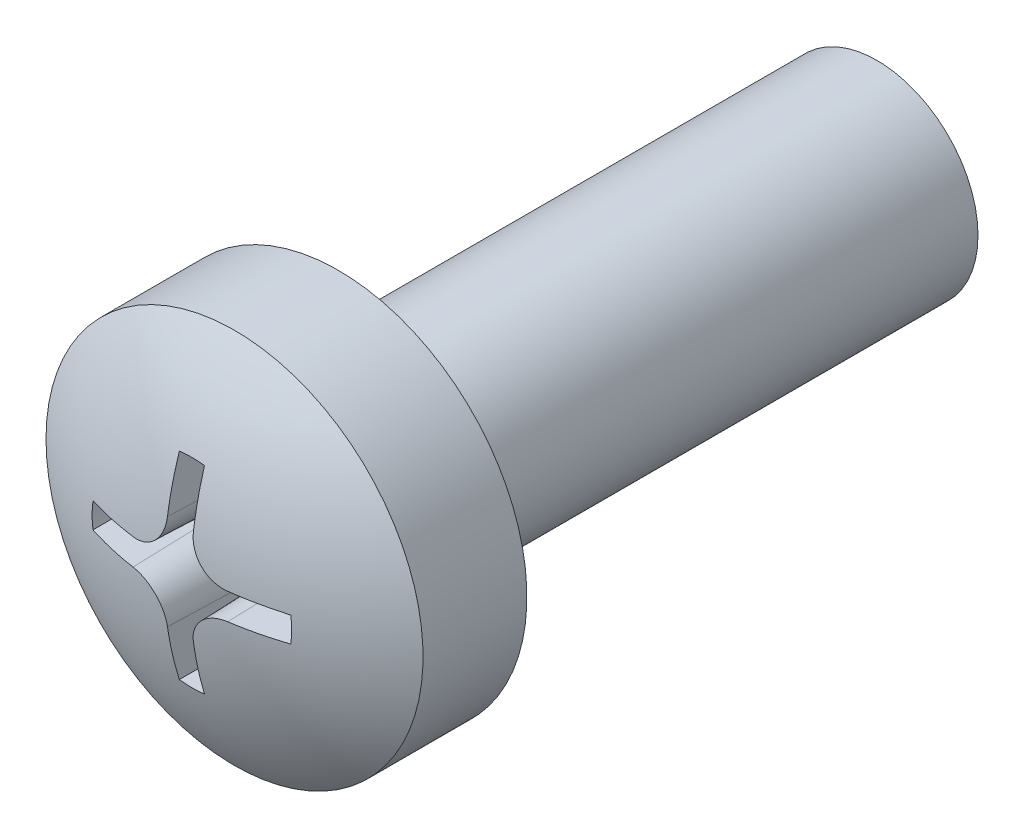
SolidWorks part; units mm, degrees
material "镍"
ref_plane "Plane1" through (0, 0, 0) normal (0, 0, 1) x (1, 0, 0)
ref_plane "Plane2" through (0, 0, 0) normal (0, 1, 0) x (1, 0, 0)
ref_plane "Plane3" through (0, 0, 0) normal (1, 0, 0) x (0, 0, -1)
sketch "Sketch1" plane through (0, 0, 0) normal (0, 0, 1) x (1, 0, 0)
  circle A0 centre (0, 0) radius 1.5
  dimension "D1" = 3
extrude "Base-Extrude" add sketch "Sketch1" along normal blind 8
sketch "Sketch6" plane through (0, 0, 0) normal (0, 1, 0) x (1, 0, 0)
  line L0 (0, 0.3936) -> (0, -34.4908) construction
  line L1 (0, -8) -> (0, 0) construction
  line L2 (0, -8) -> (2.8, -8)
  line L3 (2.8, -8) -> (2.8, -9.5425)
  line L4 (0, -10.4) -> (0, -8)
  line L5 (-1.5, -8) -> (1.5, -8) construction
  arc A0 (2.8, -9.5425) -> (0, -10.4) centre (0, -5.4) cw
  dimension "D1" = 2.4
  dimension "D9" = 5
  dimension "D8" = 2.8
revolve "Boss-Revolve2" add sketch "Sketch6" angle 360 about L0
ref_plane "Plane6" through (0, 0, 10.7) normal (0, 0, -1) x (-1, 0, 0)
sketch "Sketch7" plane through (0, 0, 10.7) normal (0, 0, -1) x (-1, 0, 0)
  line L0 (-7.1, 0) -> (5.9, 0) construction
  line L1 (0, 7.5) -> (0, -7) construction
  line L2 (0.205, 1.4859) -> (0.205, 0.7082)
  line L3 (0, 0) -> (4.9858, 4.9858) construction
  line L4 (1.4859, 0.205) -> (0.703, 0.2082)
  line L5 (1.4859, -0.205) -> (0.703, -0.2082)
  line L6 (0.205, -1.4859) -> (0.205, -0.7082)
  line L7 (-0.205, -1.4859) -> (-0.205, -0.7082)
  line L8 (-1.4859, -0.205) -> (-0.703, -0.2082)
  line L9 (-1.4859, 0.205) -> (-0.703, 0.2082)
  line L10 (-0.205, 1.4859) -> (-0.205, 0.7082)
  arc A0 (-0.205, 1.4859) -> (0.205, 1.4859) centre (0, 0) cw
  arc A1 (1.4859, -0.205) -> (1.4859, 0.205) centre (0, 0) ccw
  arc A2 (0.205, 0.7082) -> (0.703, 0.2082) centre (0.705, 0.7082) ccw
  arc A3 (-0.205, 0.7082) -> (-0.703, 0.2082) centre (-0.705, 0.7082) cw
  arc A4 (-0.205, -1.4859) -> (0.205, -1.4859) centre (0, 0) ccw
  arc A5 (-0.205, -0.7082) -> (-0.703, -0.2082) centre (-0.705, -0.7082) ccw
  arc A6 (-1.4859, -0.205) -> (-1.4859, 0.205) centre (0, 0) cw
  arc A7 (0.703, -0.2082) -> (0.205, -0.7082) centre (0.705, -0.7082) ccw
  dimension "D1" = 0.5
  dimension "D10" = 1.5
  dimension "D11" = 0.41
extrude "Cut-Extrude1" cut sketch "Sketch7" along normal blind 1.8 draft 2
